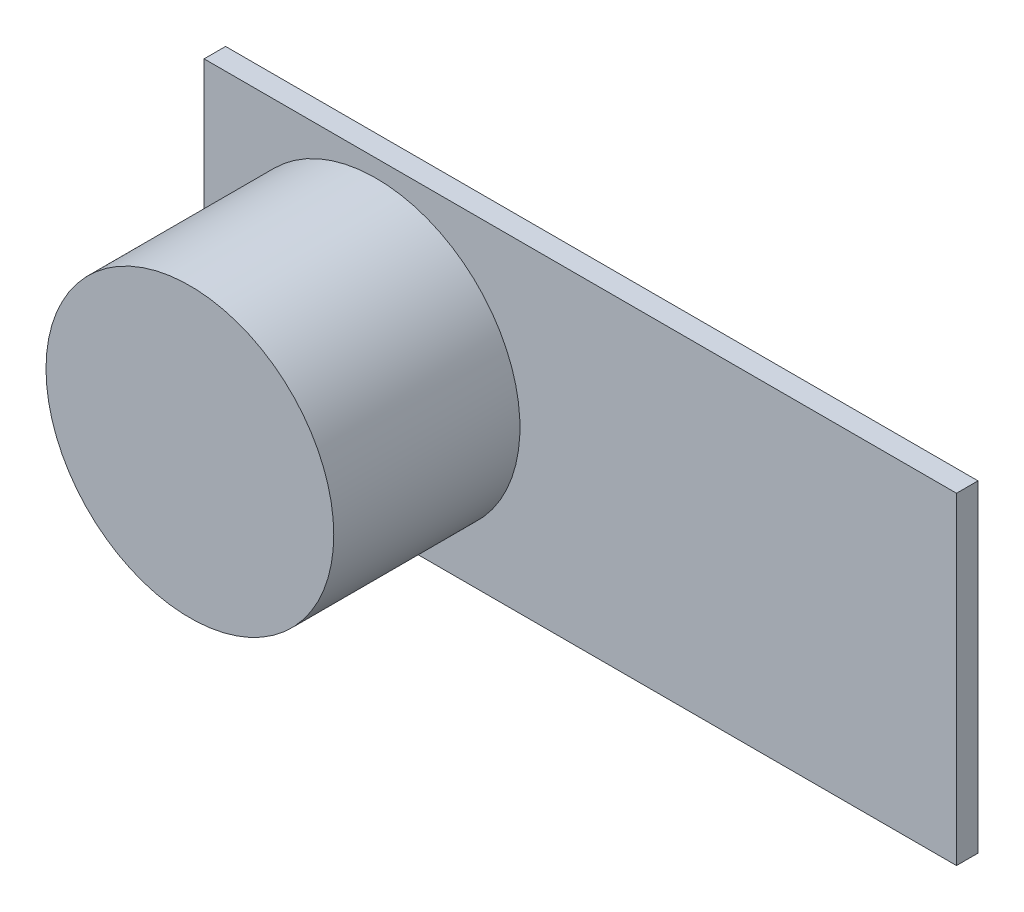
SolidWorks part; units mm, degrees
ref_plane "Front Plane" through (0, 0, 0) normal (0, 0, 1) x (1, 0, 0)
ref_plane "Top Plane" through (0, 0, 0) normal (0, 1, 0) x (1, 0, 0)
ref_plane "Right Plane" through (0, 0, 0) normal (1, 0, 0) x (0, 0, -1)
sketch "Sketch1" plane through (0, 0, 0) normal (0, 0, 1) x (1, 0, 0)
  line L1 (0, 0) -> (44.45, 0)
  line L2 (0, 0) -> (0, 19.05)
  line L3 (0, 19.05) -> (44.45, 19.05)
  line L4 (44.45, 0) -> (44.45, 19.05)
  dimension "D1" = 44.45
  dimension "D2" = 19.05
extrude "Boss-Extrude1" add sketch "Sketch1" along normal blind 1.27
sketch "Sketch2" plane through (0, 0, 1.27) normal (0, 0, 1) x (1, 0, 0)
  line L2 (0, 19.05) -> (0, 0) construction
  line L3 (0, 9.525) -> (10.16, 9.525) construction
  circle A0 centre (10.16, 9.525) radius 8.5
  point P4 (0, 9.525)
  dimension "D1" = 10.16
  dimension "D3" = 17
extrude "Boss-Extrude2" add sketch "Sketch2" along normal blind 11
